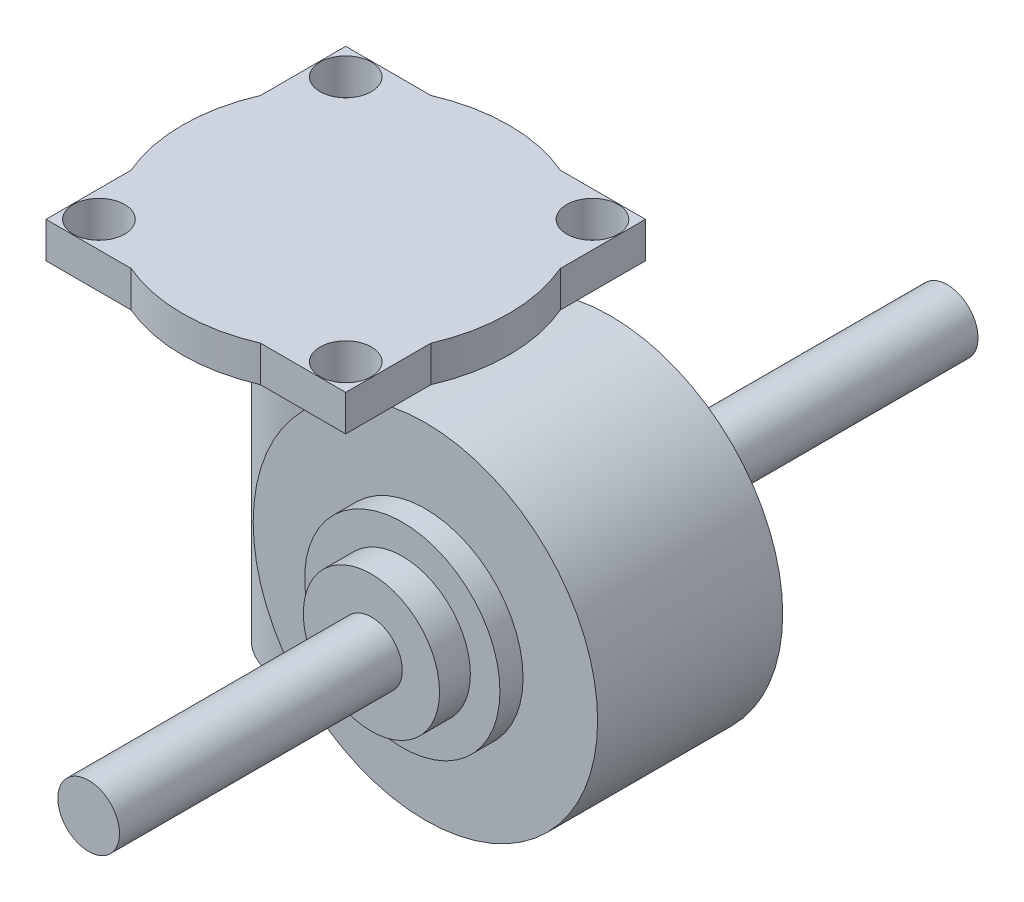
SolidWorks part; units mm, degrees
ref_plane "Ebene vorne" through (0, 0, 0) normal (0, 0, 1) x (1, 0, 0)
ref_plane "Ebene oben" through (0, 0, 0) normal (0, 1, 0) x (1, 0, 0)
ref_plane "Ebene rechts" through (0, 0, 0) normal (1, 0, 0) x (0, 0, -1)
sketch "Skizze1" plane through (0, 0, 0) normal (0, 0, 1) x (1, 0, 0)
  circle A0 centre (0, 0) radius 33.5
  dimension "D1" = 67
extrude "Aufsatz-Linear austragen1" add sketch "Skizze1" along normal blind 36
sketch "Skizze2" plane through (0, 0, 36) normal (0, 0, 1) x (1, 0, 0)
  circle A0 centre (0, 0) radius 19
  dimension "D1" = 38
extrude "Aufsatz-Linear austragen2" add sketch "Skizze2" along normal blind 4.5
sketch "Skizze3" plane through (0, 0, 40.5) normal (0, 0, 1) x (1, 0, 0)
  circle A0 centre (0, 0) radius 13.25
  dimension "D1" = 26.5
extrude "Aufsatz-Linear austragen3" add sketch "Skizze3" along normal blind 6
sketch "Skizze4" plane through (0, 0, 0) normal (0, 1, 0) x (1, 0, 0)
  line L0 (0, 0) -> (-33.5, 0)
  line L1 (-33.5, 0) -> (-33.5, -36) construction
  line L2 (-33.5, 0) -> (-33.5, -36)
  circle A0 centre (-33.5, -18) radius 13
  dimension "D1" = 26
extrude "Aufsatz-Linear austragen4" add sketch "Skizze4" along normal blind 26 and the other way blind 29 contours A0
sketch "Skizze5" plane through (0, 26, 0) normal (0, 1, 0) x (1, 0, 0)
  circle A0 centre (-33.5, -18) radius 20
  dimension "D1" = 40
extrude "Aufsatz-Linear austragen5" add sketch "Skizze5" along normal blind 9
sketch "Skizze6" plane through (0, 35, 0) normal (0, 1, 0) x (1, 0, 0)
  circle A0 centre (-33.5, -18) radius 31.75
  dimension "D1" = 63.5
extrude "Aufsatz-Linear austragen6" add sketch "Skizze6" along normal blind 7
sketch "Skizze7" plane through (0, 42, 0) normal (0, 1, 0) x (1, 0, 0)
  line L5 (-62.65, -47.15) -> (-4.35, -47.15)
  line L6 (-62.65, -47.15) -> (-62.65, 11.15)
  line L7 (-62.65, 11.15) -> (-4.35, 11.15)
  line L8 (-4.35, -47.15) -> (-4.35, 11.15)
  line L9 (-62.65, -47.15) -> (-4.35, 11.15) construction
  line L10 (-62.65, 11.15) -> (-4.35, -47.15) construction
  point P6 (-33.5, -18)
  dimension "D1" = 58.3
  dimension "D2" = 58.3
extrude "Aufsatz-Linear austragen7" add sketch "Skizze7" against normal blind 7
sketch "Skizze8" plane through (0, 42, 0) normal (0, 1, 0) x (1, 0, 0)
  line L1 (-57.5, -42) -> (-9.5, -42)
  line L2 (-57.5, -42) -> (-57.5, 6)
  line L3 (-57.5, 6) -> (-9.5, 6)
  line L4 (-9.5, -42) -> (-9.5, 6)
  line L5 (-57.5, -42) -> (-9.5, 6) construction
  line L6 (-57.5, 6) -> (-9.5, -42) construction
  point P0 (-33.5, -18)
  dimension "D1" = 48
  dimension "D2" = 48
hole_wizard "Ø10.0 (10) Durchmesser Bohrung1" positions "Skizze10" profile "Skizze9" hole size "Ø10.0" standard "ANSI Metrisch" end condition up to next
sketch "Skizze10" plane through (0, 42, 0) normal (0, 1, 0) x (1, 0, 0)
  point P0 (-57.5, -42)
  point P4 (-57.5, 6)
  point P7 (-9.5, 6)
  point P10 (-9.5, -42)
sketch "Skizze9" plane through (-57.5, 42, 42) normal (1, 0, 0) x (0, 0, 1)
  line L0 (0, 0) -> (0, 7)
  line L1 (0, 7) -> (5, 7)
  line L2 (5, 7) -> (5, 0)
  line L5 (5, 0) -> (0, 0)
  line L11 (0, -6.35) -> (0, 107.95) construction
  dimension "Bohrerdurchmesser" = 10
  dimension "Bohrungstiefe" = 7
sketch "Skizze13" plane through (0, 0, 0) normal (0, 0, -1) x (-1, 0, 0)
  circle A0 centre (0, 0) radius 19
  dimension "D1" = 38
extrude "Aufsatz-Linear austragen8" add sketch "Skizze13" along normal blind 4.5 contours A0
sketch "Skizze14" plane through (0, 0, -4.5) normal (0, 0, -1) x (-1, 0, 0)
  circle A0 centre (0, 0) radius 13.25
  dimension "D1" = 26.5
extrude "Aufsatz-Linear austragen9" add sketch "Skizze14" along normal blind 6 contours A0
sketch "Skizze15" plane through (0, 0, -10.5) normal (0, 0, -1) x (-1, 0, 0)
  circle A0 centre (0, 0) radius 6
  dimension "D1" = 12
extrude "Aufsatz-Linear austragen10" add sketch "Skizze15" along normal blind 55 contours A0
sketch "Skizze16" plane through (0, 0, 46.5) normal (0, 0, 1) x (1, 0, 0)
  circle A0 centre (0, 0) radius 6
  dimension "D1" = 12
extrude "Aufsatz-Linear austragen11" add sketch "Skizze16" along normal blind 55
